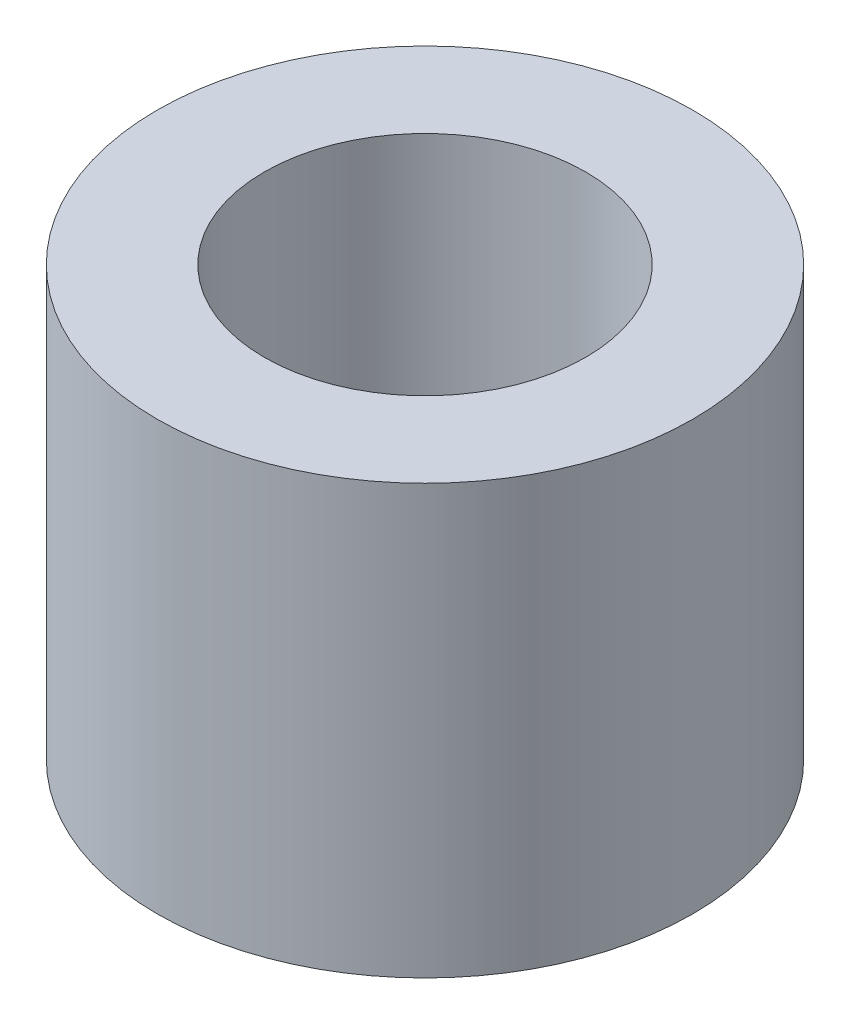
SolidWorks part; units mm, degrees
material "Nylon 101"
ref_plane "Front Plane" through (0, 0, 0) normal (0, 0, 1) x (1, 0, 0)
ref_plane "Top Plane" through (0, 0, 0) normal (0, 1, 0) x (1, 0, 0)
ref_plane "Right Plane" through (0, 0, 0) normal (1, 0, 0) x (0, 0, -1)
sketch "Sketch1" plane through (0, 0, 0) normal (0, 1, 0) x (1, 0, 0)
  circle A0 centre (0, 0) radius 1.905
  circle A1 centre (0, 0) radius 3.175
  dimension "D1" = 3.81
  dimension "D2" = 6.35
extrude "Boss-Extrude1" add sketch "Sketch1" along normal blind 5.08
